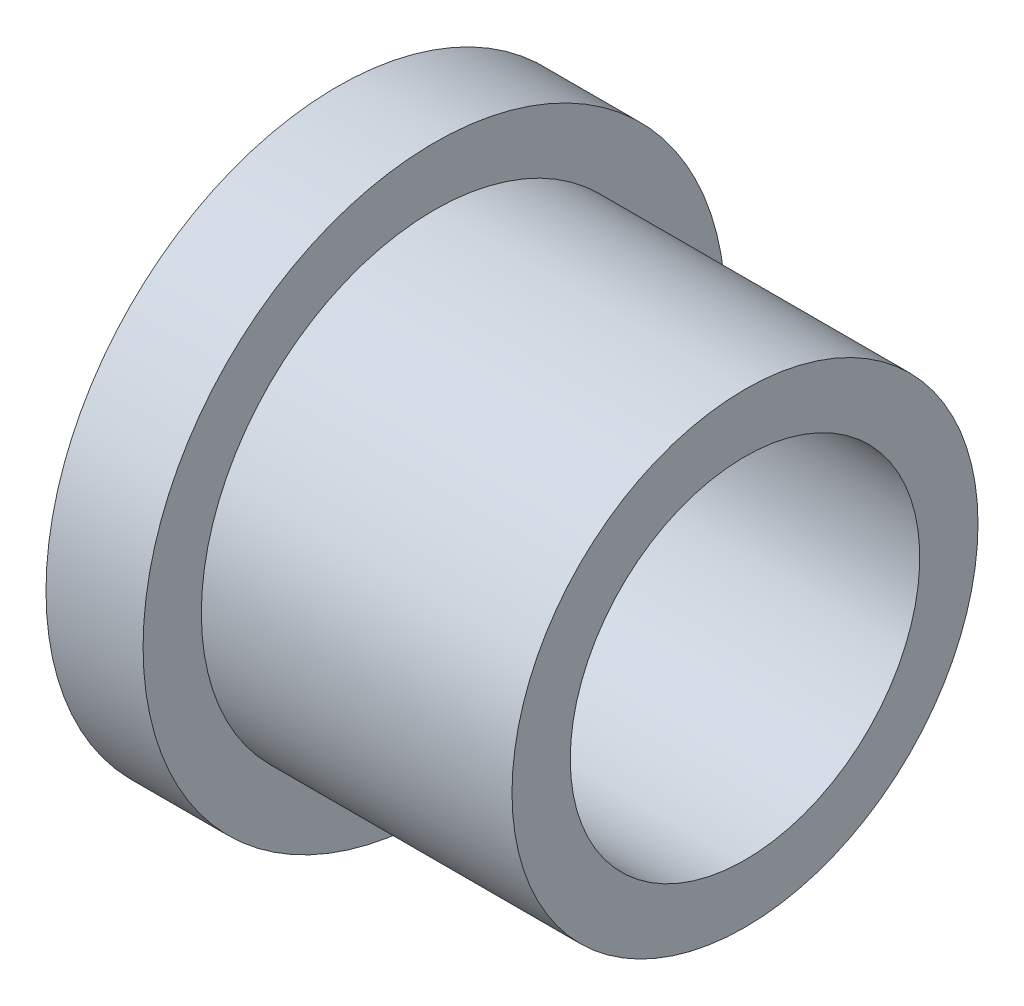
SolidWorks part; units mm, degrees
ref_plane "Front Plane" through (0, 0, 0) normal (0, 0, 1) x (1, 0, 0)
ref_plane "Top Plane" through (0, 0, 0) normal (0, 1, 0) x (1, 0, 0)
ref_plane "Right Plane" through (0, 0, 0) normal (1, 0, 0) x (0, 0, -1)
sketch "Sketch1" plane through (0, 0, 0) normal (0, 1, 0) x (1, 0, 0)
  line L0 (0, 0) -> (69.1845, 0) construction
  line L1 (0, 15) -> (0, 9)
  line L2 (0, 15) -> (5, 15)
  line L3 (5, 15) -> (5, 12)
  line L4 (5, 12) -> (21, 12)
  line L5 (21, 12) -> (21, 9)
  line L6 (5, 9) -> (21, 9)
  line L7 (5, 9) -> (0, 9)
revolve "Revolve1" add sketch "Sketch1" angle 360 about L0
